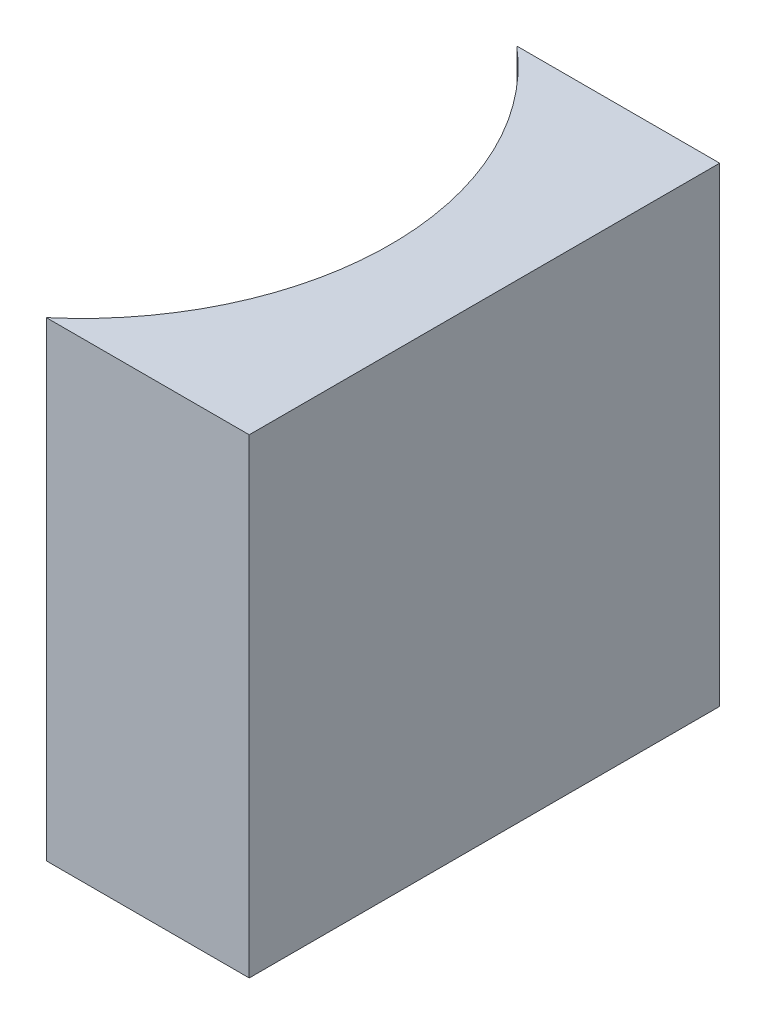
SolidWorks part; units mm, degrees
ref_plane "前视基准面" through (0, 0, 0) normal (0, 0, 1) x (1, 0, 0)
ref_plane "上视基准面" through (0, 0, 0) normal (0, 1, 0) x (1, 0, 0)
ref_plane "右视基准面" through (0, 0, 0) normal (1, 0, 0) x (0, 0, -1)
sketch "草图1" plane through (0, 0, 0) normal (0, 1, 0) x (1, 0, 0)
  line L0 (0, 0) -> (0, -10)
  line L1 (0, 0) -> (-4.3134, 0)
  line L2 (0, -10) -> (-4.3134, -10)
  line L3 (0.664, -5) -> (-9.4659, -5) construction
  arc A0 (-4.3134, -10) -> (-4.3134, 0) centre (-8.56, -5) ccw
  point P7 (-2, -5)
  point P8 (0, -5)
  dimension "D2" = 6.56
  dimension "D3" = 2
  dimension "D1" = 10
extrude "凸台-拉伸1" add sketch "草图1" along normal blind 10
